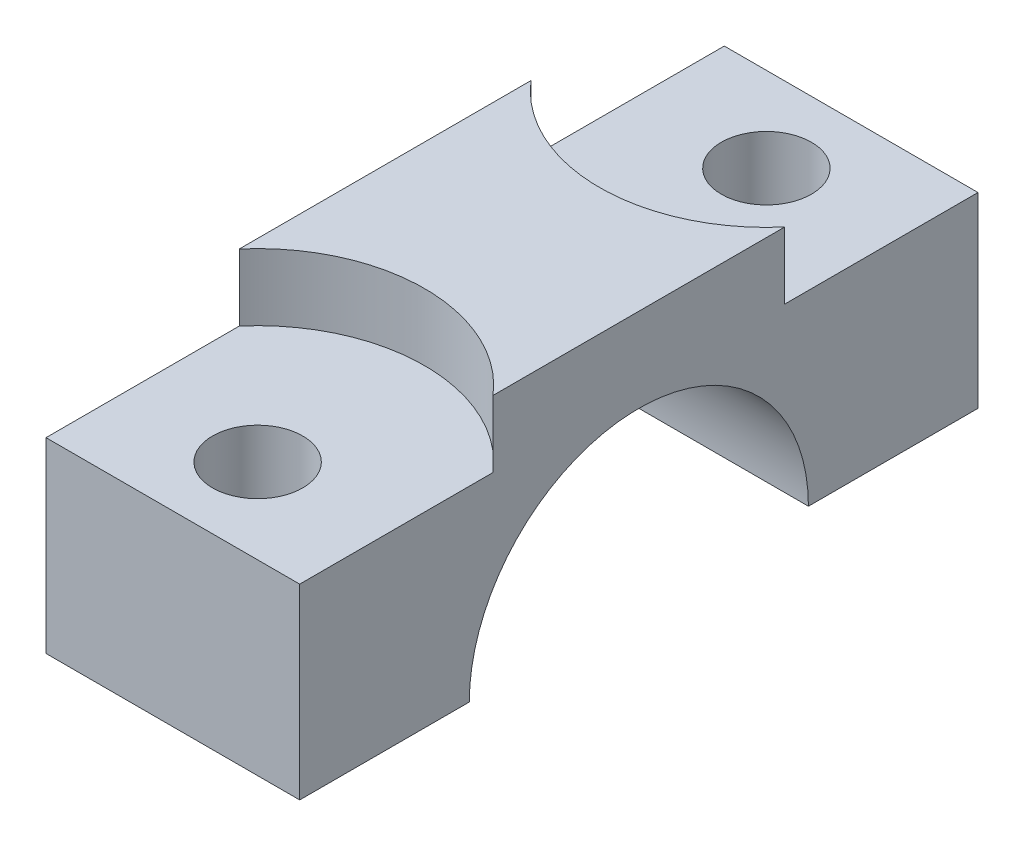
SolidWorks part; units mm, degrees
ref_plane "Front Plane" through (0, 0, 0) normal (0, 0, 1) x (1, 0, 0)
ref_plane "Top Plane" through (0, 0, 0) normal (0, 1, 0) x (1, 0, 0)
ref_plane "Right Plane" through (0, 0, 0) normal (1, 0, 0) x (0, 0, -1)
sketch "Sketch1" plane through (0, 0, 0) normal (1, 0, 0) x (0, 0, -1)
  line L0 (12.7, 0) -> (25.4, 0)
  line L1 (-25.4, 19) -> (25.4, 19)
  line L2 (-25.4, 19) -> (-25.4, 0)
  line L3 (-25.4, 0) -> (-12.7, 0)
  line L4 (25.4, 19) -> (25.4, 0)
  line L5 (-25.4, 19) -> (25.4, 0) construction
  line L6 (-25.4, 0) -> (25.4, 19) construction
  arc A0 (-12.7, 0) -> (12.7, 0) centre (0, 0) cw
  point P0 (0, 9.5)
  point P10 (0, 19)
  dimension "D3" = 12.7
  dimension "D1" = 50.8
  dimension "D2" = 19
extrude "Boss-Extrude1" add sketch "Sketch1" along normal mid plane 19 contours L2 L3 A0 L0 L4 L1
sketch "Sketch2" plane through (0, 0, 0) normal (0, -1, 0) x (1, 0, 0)
  line L0 (-9.5, 19.05) -> (9.5, 19.05) construction
  line L1 (-9.5, 25.4) -> (-9.5, 12.7) construction
  line L2 (9.5, 25.4) -> (9.5, 12.7) construction
  line L3 (-9.5, -19.05) -> (9.5, -19.05) construction
  line L4 (-9.5, -12.7) -> (-9.5, -25.4) construction
  line L5 (9.5, -12.7) -> (9.5, -25.4) construction
  point P12 (0, 19.05)
  point P13 (0, -19.05)
sketch "Sketch3" plane through (0, 19, 0) normal (0, 1, 0) x (1, 0, 0)
  point P0 (0, -19.05)
  point P3 (0, 19.05)
hole_wizard "CBORE for M12 Hex Head Cap Screw1" positions "Sketch3" profile "Sketch4" counterbore size "M12" standard "ISO" end condition through all
sketch "Sketch4" plane through (0, 19, 19.05) normal (1, 0, 0) x (0, 0, 1)
  line L0 (0, 0) -> (0, 19)
  line L1 (0, 19) -> (3.375, 19)
  line L3 (3.375, 19) -> (3.375, 5)
  line L4 (3.375, 5) -> (12.5, 5)
  line L5 (12.5, 5) -> (12.5, 0)
  line L7 (12.5, 0) -> (0, 0)
  line L11 (0, -6.35) -> (0, 107.95) construction
  dimension "Thru Hole Dia." = 6.75
  dimension "Thru Hole Depth" = 19
  dimension "C'Bore Dia." = 25
  dimension "C'Bore Depth" = 5
